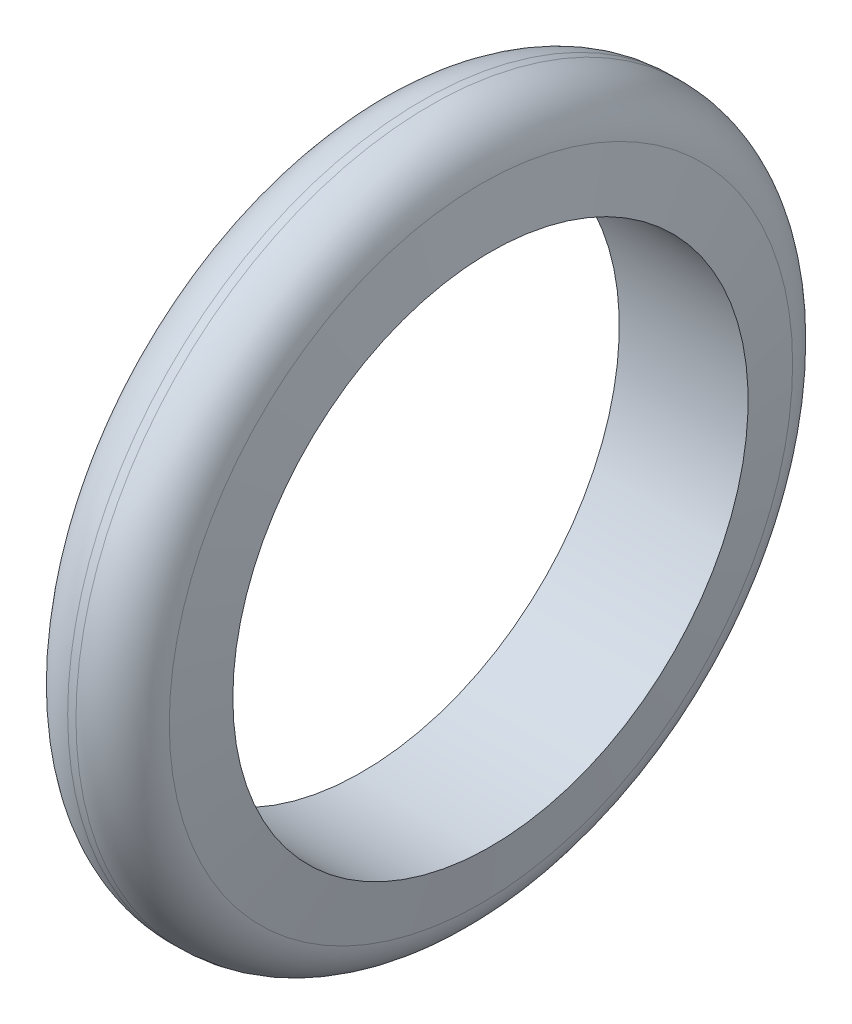
SolidWorks part; units mm, degrees
ref_plane "Front Plane" through (0, 0, 0) normal (0, 0, 1) x (1, 0, 0)
ref_plane "Top Plane" through (0, 0, 0) normal (0, 1, 0) x (1, 0, 0)
ref_plane "Right Plane" through (0, 0, 0) normal (1, 0, 0) x (0, 0, -1)
sketch "Sketch1" plane through (0, 0, 0) normal (0, 0, 1) x (1, 0, 0)
  line L0 (0, 0) -> (44.6778, 0) construction
  line L1 (0, 0) -> (0, 40) construction
  line L2 (-10, 40) -> (10, 40)
  line L3 (10, 40) -> (7.3551, 55)
  line L4 (7.3551, 55) -> (-7.3551, 55)
  line L5 (-7.3551, 55) -> (-10, 40)
  point P6 (11.3404, 40)
  point P9 (0, 0)
  point P10 (0, 0)
  point P11 (6.5862, 40)
  point P12 (0, 0)
  point P13 (0, 0)
  point P14 (10.1994, 40)
  dimension "D1" = 80
  dimension "D2" = 110
  dimension "D3" = 20
  dimension "D4" = 10
revolve "Revolve1" add sketch "Sketch1" angle 360 about L0
fillet "Fillet1" radius 8 1 edges at (7.3551, 0, 55)
fillet "Fillet2" radius 8 1 edges at (-7.3551, 0, 55)
